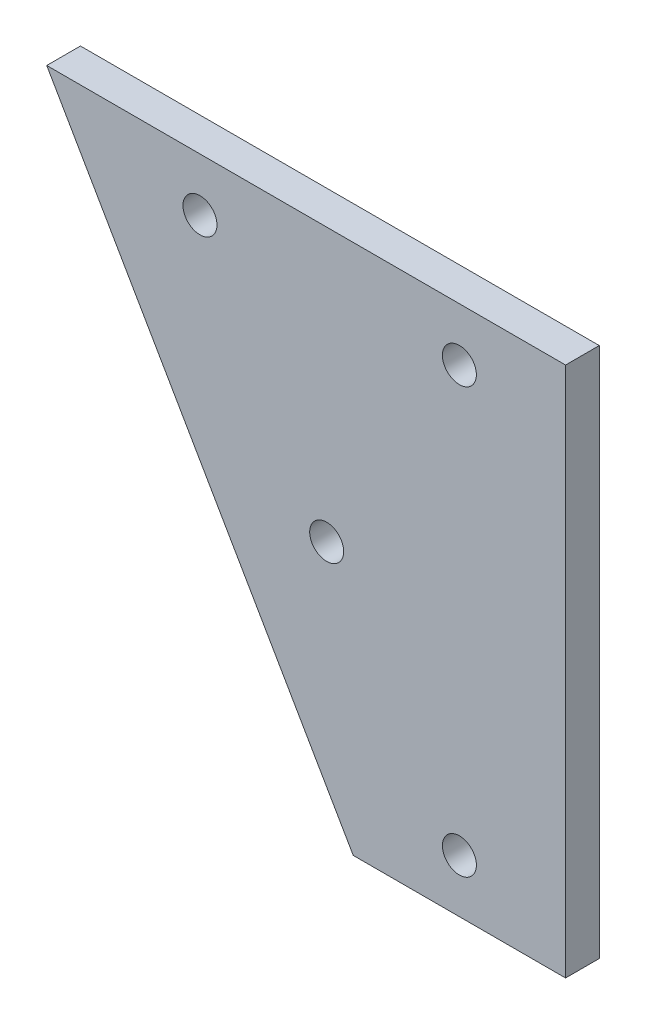
SolidWorks part; units mm, degrees
ref_plane "Front Plane" through (0, 0, 0) normal (0, 0, 1) x (1, 0, 0)
ref_plane "Top Plane" through (0, 0, 0) normal (0, 1, 0) x (1, 0, 0)
ref_plane "Right Plane" through (0, 0, 0) normal (1, 0, 0) x (0, 0, -1)
sketch "Sketch1" plane through (0, 0, 0) normal (0, 0, 1) x (1, 0, 0)
  line L0 (0, 0) -> (48.8675, 0)
  line L2 (28.8675, -50) -> (0, 0)
  line L3 (48.8675, 0) -> (48.8675, -50)
  line L4 (48.8675, -50) -> (28.8675, -50)
  line L5 (28.8675, -50) -> (28.8675, 0) construction
  line L6 (28.8675, -10) -> (23.094, 0) construction
  line L7 (11.547, 0) -> (28.8675, -30) construction
  line L8 (38.8675, 0) -> (38.8675, -50) construction
  circle A0 centre (38.8675, -5) radius 1.6
  circle A1 centre (38.8675, -45) radius 1.6
  circle A2 centre (14.4338, -5) radius 1.6
  circle A3 centre (26.3675, -25.6699) radius 1.6
  dimension "D6" = 5
  dimension "D7" = 3.2
  dimension "D8" = 5
  dimension "D9" = 40
  dimension "D1" = 30
  dimension "D2" = 20
  dimension "D3" = 20
  dimension "D4" = 10
  dimension "D5" = 10
  dimension "D10" = 5
extrude "Boss-Extrude1" add sketch "Sketch1" along normal blind 3.175
